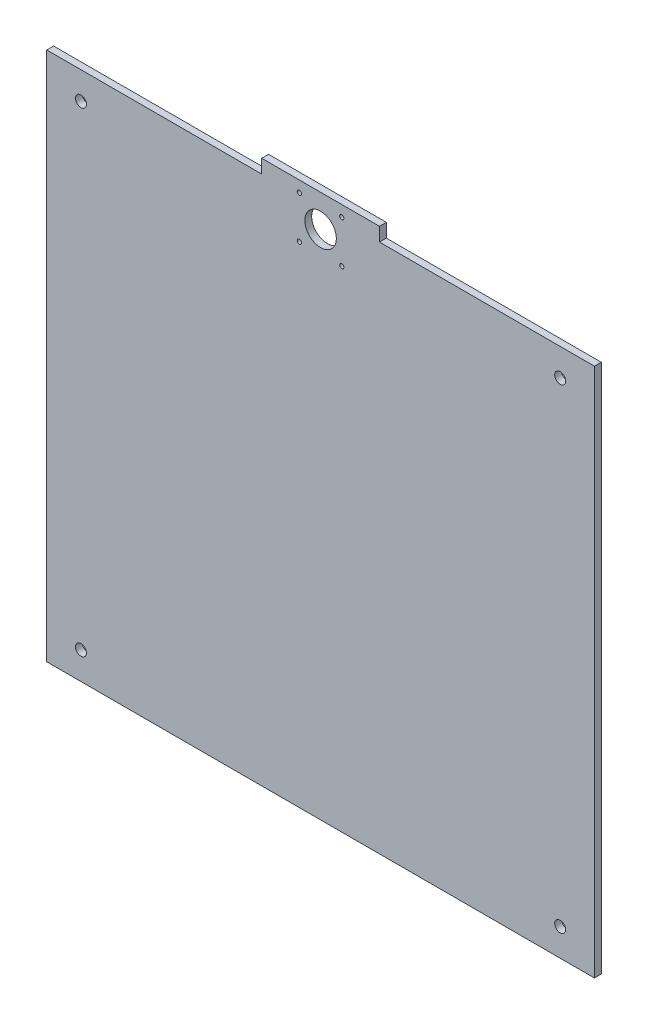
SolidWorks part; units mm, degrees
ref_plane "Plan de face" through (0, 0, 0) normal (0, 0, 1) x (1, 0, 0)
ref_plane "Plan de dessus" through (0, 0, 0) normal (0, 1, 0) x (1, 0, 0)
ref_plane "Plan de droite" through (0, 0, 0) normal (1, 0, 0) x (0, 0, -1)
sketch "Sketch1" plane through (0, 0, 0) normal (0, 0, 1) x (1, 0, 0)
  line L1 (0, 0) -> (400, 0)
  line L2 (0, 0) -> (0, 397)
  line L3 (0, 397) -> (400, 397)
  line L4 (400, 0) -> (400, 397)
  dimension "D1" = 400
  dimension "D2" = 397
extrude "Boss-Extrude1" add sketch "Sketch1" along normal blind 5
sketch "Sketch2" plane through (0, 0, 5) normal (0, 0, 1) x (1, 0, 0)
  line L0 (200, 0) -> (200, 397) construction
  line L1 (0, 0) -> (400, 0) construction
  line L2 (400, 397) -> (0, 397) construction
  circle A0 centre (215.5, 389) radius 1.55
  circle A1 centre (215.5, 358) radius 1.55
  circle A2 centre (184.5, 358) radius 1.55
  circle A3 centre (184.5, 389) radius 1.55
  dimension "D1" = 3.1
  dimension "D2" = 3.1
  dimension "D3" = 31
  dimension "D4" = 15.5
  dimension "D5" = 8
extrude "Cut-Extrude1" cut sketch "Sketch2" against normal through all
sketch "Sketch3" plane through (0, 0, 5) normal (0, 0, 1) x (1, 0, 0)
  line L0 (215.5, 389) -> (184.5, 358) construction
  line L1 (215.5, 358) -> (184.5, 389) construction
  circle A0 centre (200, 373.5) radius 11.5
  dimension "D1" = 23
extrude "Cut-Extrude2" cut sketch "Sketch3" against normal through all
sketch "Sketch4" plane through (0, 0, 5) normal (0, 0, 1) x (1, 0, 0)
  line L0 (400, 387) -> (243, 387)
  line L1 (400, 0) -> (400, 397) construction
  line L2 (243, 387) -> (243, 397)
  line L3 (400, 397) -> (0, 397) construction
  line L4 (243, 397) -> (400, 397)
  line L5 (400, 397) -> (400, 387)
  line L7 (200, 397) -> (200, 0) construction
  line L8 (0, 0) -> (400, 0) construction
  line L9 (0, 397) -> (0, 387)
  line L10 (157, 397) -> (0, 397)
  line L11 (157, 387) -> (157, 397)
  line L12 (0, 387) -> (157, 387)
  dimension "D1" = 10
  dimension "D2" = 0
  dimension "D3" = 157
extrude "Cut-Extrude3" cut sketch "Sketch4" against normal through all
ref_plane "Plane1" through (200, 0, 0) normal (1, 0, 0) x (0, 0, -1)
fillet "Fillet1" [suppressed] radius 5
fillet "Fillet2" [suppressed] radius 5
sketch "Sketch5" plane through (0, 0, 5) normal (0, 0, 1) x (1, 0, 0)
  line L0 (0, 387) -> (0, 0) construction
  line L1 (0, 387) -> (157, 387) construction
  line L4 (200, 0) -> (200, 397) construction
  line L5 (0, 0) -> (400, 0) construction
  line L6 (243, 397) -> (157, 397) construction
  circle A0 centre (25, 367.03) radius 4
  circle A1 centre (25, 20.03) radius 4
  circle A2 centre (375, 20.03) radius 4
  circle A3 centre (375, 367.03) radius 4
  dimension "D2" = 8
  dimension "D5" = 8
  dimension "D1" = 25
  dimension "D3" = 19.97
  dimension "D4" = 25
  dimension "D6" = 20.03
extrude "Cut-Extrude4" cut sketch "Sketch5" against normal up to surface (5 mm away) up to face at (200, 292.75, 0)
equation "\"D2@Sketch2\"=\"D1@Sketch2\""
